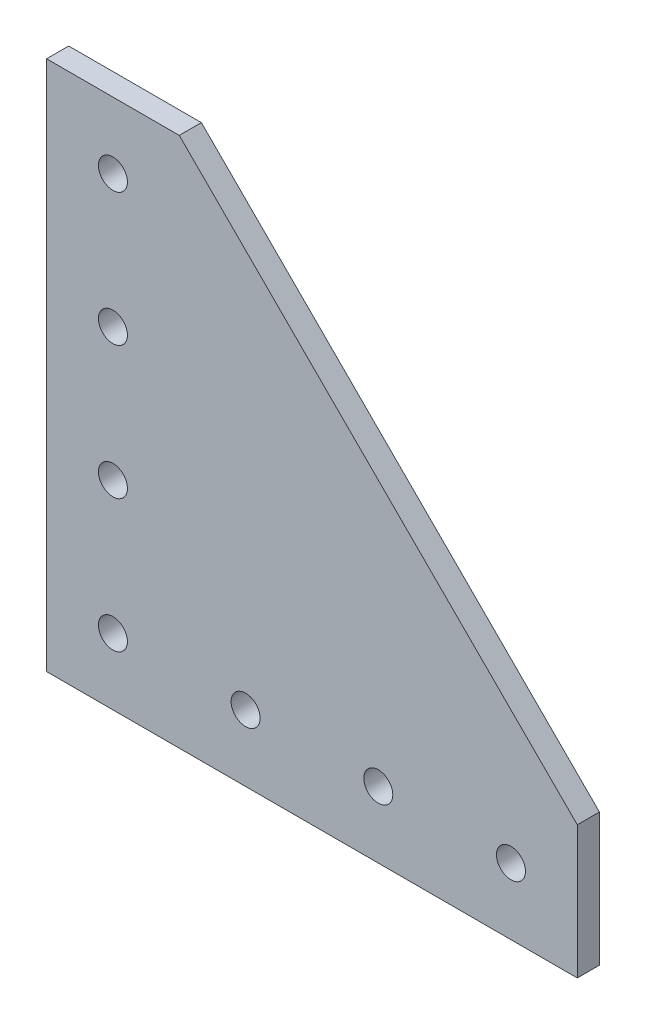
SolidWorks part; units mm, degrees
ref_plane "Front Plane" through (0, 0, 0) normal (0, 0, 1) x (1, 0, 0)
ref_plane "Top Plane" through (0, 0, 0) normal (0, 1, 0) x (1, 0, 0)
ref_plane "Right Plane" through (0, 0, 0) normal (1, 0, 0) x (0, 0, -1)
sketch "Sketch1" plane through (0, 0, 0) normal (0, 0, 1) x (1, 0, 0)
  line L0 (-76.2, -76.2) -> (76.2, -76.2) construction
  line L1 (-76.2, 76.2) -> (-76.2, -76.2) construction
  line L2 (76.2, -76.2) -> (76.2, -38.1) construction
  line L3 (-57.15, -52.9844) -> (-57.15, -61.3156) construction
  point P3 (0, -76.2)
  point P8 (-76.2, 0)
  point P9 (-57.15, -57.15)
  point P10 (76.2, -57.15)
  point P11 (0, 25.4)
  point P12 (-19.05, -57.15)
sketch "Sketch2" plane through (0, 0, 0) normal (1, 0, 0) x (0, 0, -1)
  line L0 (3.175, 0) -> (-3.175, 0) construction
  point P4 (0, 0)
  dimension "Thickness" = 6.35
sketch "Sketch3" plane through (0, 0, 0) normal (0, 0, 1) x (1, 0, 0)
  line L0 (76.2, -38.1) -> (76.2, -76.2)
  line L1 (76.2, -76.2) -> (-76.2, -76.2)
  line L2 (-76.2, -76.2) -> (-76.2, 76.2)
  line L3 (-76.2, 76.2) -> (-38.1, 76.2)
  line L4 (-38.1, 76.2) -> (76.2, -38.1)
extrude "Boss-Extrude1" add sketch "Sketch3" against normal up to vertex (3.175 mm away) and the other way up to vertex (3.175 mm away) up to point (0, 0, -3.175) other way up to point (0, 0, 3.175)
sketch "Sketch4" plane through (0, 0, 3.175) normal (0, 0, 1) x (1, 0, 0)
  line L0 (-57.15, -52.9844) -> (-57.15, -61.3156) construction
  line L1 (-76.2, -76.2) -> (0, 0) construction
  line L2 (-57.15, -57.15) -> (-19.05, -57.15) construction
  line L3 (-57.15, -57.15) -> (-57.15, -19.05) construction
  circle A0 centre (-57.15, -57.15) radius 4.1656
  circle A5 centre (-19.05, -57.15) radius 4.1656
  circle A6 centre (19.05, -57.15) radius 4.1656
  circle A7 centre (-57.15, -19.05) radius 4.1656
  circle A8 centre (-57.15, 19.05) radius 4.1656
  circle A9 centre (57.15, -57.15) radius 4.1656
  circle A10 centre (-57.15, 57.15) radius 4.1656
  dimension "D2" = 38.1
  dimension "D4" = 38.1
  dimension "D1" = 4
  dimension "D3" = 4
extrude "Cut-Extrude1" cut sketch "Sketch4" against normal through all
equation "\"D2@Sketch4\"=\"Hole Spacing@Sketch1\""
equation "\"D1@Sketch4\"=\"#Holes@Sketch1\""
equation "\"D4@Sketch4\"=\"Hole Spacing@Sketch1\""
equation "\"D3@Sketch4\"=\"#Holes@Sketch1\""
